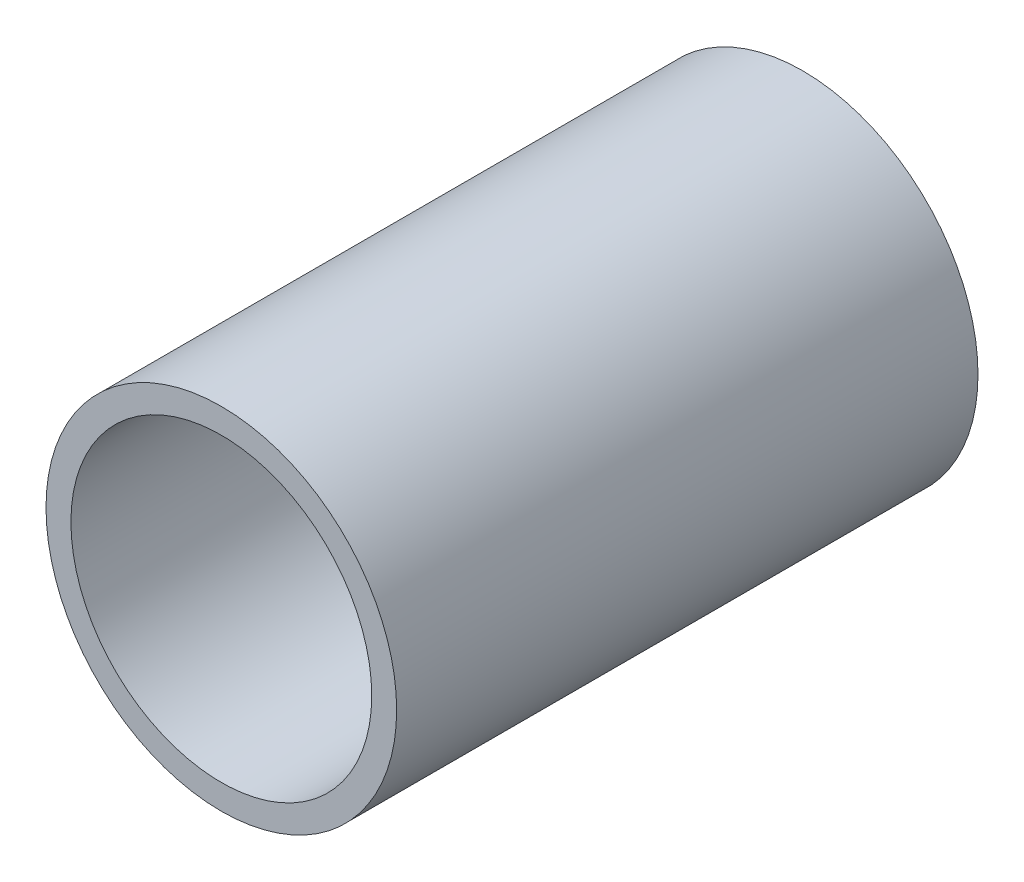
SolidWorks part; units mm, degrees
ref_plane "Płaszczyzna przednia" through (0, 0, 0) normal (0, 0, 1) x (1, 0, 0)
ref_plane "Płaszczyzna górna" through (0, 0, 0) normal (0, 1, 0) x (1, 0, 0)
ref_plane "Płaszczyzna prawa" through (0, 0, 0) normal (1, 0, 0) x (0, 0, -1)
sketch "Szkic1" plane through (0, 0, 0) normal (0, 0, 1) x (1, 0, 0)
  circle A0 centre (0, 0) radius 8.15
  circle A1 centre (0, 0) radius 9.5
extrude "Dodanie-wyciągnięcie1" add sketch "Szkic1" along normal blind 31.5
